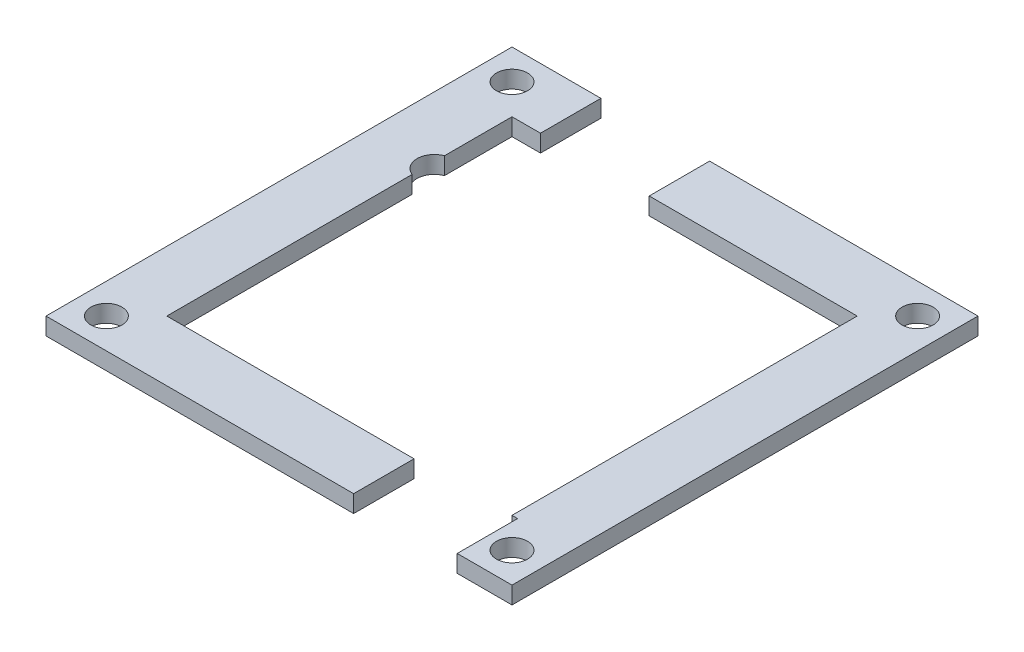
SolidWorks part; units mm, degrees
ref_plane "Front" through (0, 0, 0) normal (0, 0, 1) x (1, 0, 0)
ref_plane "Top" through (0, 0, 0) normal (0, 1, 0) x (1, 0, 0)
ref_plane "Right" through (0, 0, 0) normal (1, 0, 0) x (0, 0, -1)
sketch "草图3" plane through (0, 0, 0) normal (0, 1, 0) x (1, 0, 0)
  line L0 (16.9, -20) -> (20, -20)
  line L1 (-20, -20) -> (12.4, -20)
  line L2 (20, -20) -> (20, 20)
  line L3 (-27, 27) -> (-27, -27)
  line L4 (-27, -27) -> (27, -27)
  line L5 (27, -27) -> (27, 27)
  line L6 (27, 27) -> (-27, 27)
  line L7 (-8.6, 1.7) -> (-7.6812, 1.7)
  line L8 (-5.8437, 1.7) -> (-4.925, 1.7)
  line L9 (20.65, -20) -> (20, -20)
  line L10 (16.9, -6) -> (12.4, -6)
  line L11 (12.4, -6) -> (12.4, -19.5)
  line L12 (-10.4, 20) -> (-4.1, 20)
  line L13 (16.9, -6) -> (16.9, -19.5)
  line L14 (-20, 20) -> (-20, -20)
  line L15 (-3.0875, 1.7) -> (-2.1687, 1.7)
  line L16 (-0.3312, 1.7) -> (0.5875, 1.7)
  line L17 (2.425, 1.7) -> (3.3438, 1.7)
  line L18 (5.1813, 1.7) -> (6.1, 1.7)
  line L19 (8.8563, -13.3) -> (7.9375, -13.3)
  line L20 (8.65, -20) -> (8.65, -27)
  line L21 (-8.6, 1.7) -> (-8.6, -13.3)
  line L22 (-7.6812, -13.3) -> (-8.6, -13.3)
  line L23 (-8.6, -13.3) -> (-8.6029, -13.3589)
  line L24 (-10.4375, -13.3) -> (-11.3562, -13.3)
  line L25 (-10.4375, 1.7) -> (-11.3562, 1.7)
  line L26 (6.1, 1.7) -> (6.1, -13.3)
  line L27 (-4.925, -13.3) -> (-4.925, 1.7)
  line L28 (-11.3562, -13.3) -> (-11.3562, 1.7)
  line L29 (-3.0875, -13.3) -> (-3.0875, 1.7)
  line L30 (-10.4375, -13.3) -> (-10.4375, 1.7)
  line L31 (-2.1687, -13.3) -> (-2.1687, 1.7)
  line L32 (8.8563, 1.7) -> (7.9375, 1.7)
  line L33 (-5.8437, -13.3) -> (-5.8437, 1.7)
  line L34 (8.8563, -13.3) -> (8.8563, 1.7)
  line L35 (-7.6812, -13.3) -> (-7.6812, 1.7)
  line L36 (-0.3312, -13.3) -> (-0.3312, 1.7)
  line L37 (0.5875, -13.3) -> (0.5875, 1.7)
  line L38 (5.1813, -13.3) -> (6.1, -13.3)
  line L39 (2.425, -13.3) -> (2.425, 1.7)
  line L40 (3.3438, -13.3) -> (3.3438, 1.7)
  line L41 (2.425, -13.3) -> (3.3438, -13.3)
  line L42 (5.1813, -13.3) -> (5.1813, 1.7)
  line L43 (-0.3312, -13.3) -> (0.5875, -13.3)
  line L44 (-3.0875, -13.3) -> (-2.1687, -13.3)
  line L45 (-5.8437, -13.3) -> (-4.925, -13.3)
  line L46 (7.9375, -13.3) -> (7.9375, 1.7)
  line L47 (20.65, -20) -> (20.65, -27)
  line L48 (12.4, -19.5) -> (12.4, -20)
  line L49 (16.9, -19.5) -> (16.9, -20)
  line L50 (-20, -20) -> (20, -20) construction
  line L51 (-20, 20) -> (20, 20)
  line L52 (-16.7, 20) -> (-10.4, 20)
  line L53 (20, 20) -> (-20, 20) construction
  line L54 (-16.7, 20) -> (-16.7, 27)
  line L55 (-4.1, 20) -> (-4.1, 27)
  circle A0 centre (-23.5, -23.5) radius 1.8
  circle A1 centre (23.5, -23.5) radius 1.8
  circle A2 centre (-23.5, 23.5) radius 1.8
  circle A3 centre (23.5, 23.5) radius 1.8
  circle A4 centre (-2.1, -16.5) radius 2
  circle A5 centre (-16.4, -3.7) radius 2
  circle A6 centre (-19.3, 10.3) radius 2
  circle A7 centre (-1.1, 15.8) radius 2
  point P0 (0, 0)
  point P61 (-10.8969, 1.7)
  dimension "D1" = 7
extrude "凸台-拉伸2" add sketch "草图3" along normal blind 2 contours A6 L14 L51 L54 L6 L3 L4 L20 L1 A2 A0 | L55 L51 L2 L9 L47 L4 L5 L6 A3 A1
